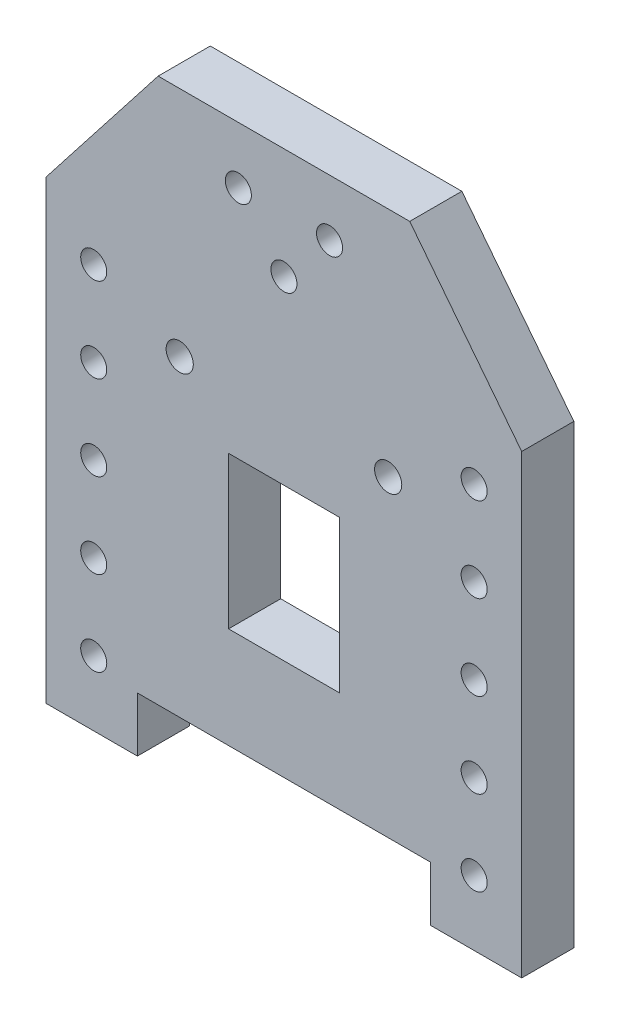
SolidWorks part; units mm, degrees
ref_plane "Plano frontal" through (0, 0, 0) normal (0, 0, 1) x (1, 0, 0)
ref_plane "Plano superior" through (0, 0, 0) normal (0, 1, 0) x (1, 0, 0)
ref_plane "Plano direito" through (0, 0, 0) normal (1, 0, 0) x (0, 0, -1)
sketch "Esboço1" plane through (0, 0, 0) normal (0, 0, 1) x (1, 0, 0)
  line L0 (0, 47.2571) -> (8.5, 47.2571)
  line L1 (0, 47.2571) -> (-8.5, 47.2571)
  line L2 (0, 23.9177) -> (8.5, 23.9177)
  line L3 (0, 23.9177) -> (-8.5, 23.9177)
  line L4 (0, 8.4) -> (0, 75) construction
  line L5 (0, 56.3545) -> (-16, 56.3545) construction
  line L6 (0, 56.3545) -> (16, 56.3545) construction
  line L7 (8.5, 47.2571) -> (8.5, 23.9177)
  line L8 (-8.5, 47.2571) -> (-8.5, 23.9177)
  line L20 (19.3117, 92) -> (-19.3117, 92)
  line L21 (-19.3117, 92) -> (-36.5, 70)
  line L22 (-36.5, 70) -> (-36.5, 0)
  line L23 (-36.5, 0) -> (-22.5, 0)
  line L24 (-22.5, 0) -> (-22.5, 8.4)
  line L25 (-22.5, 8.4) -> (22.5, 8.4)
  line L26 (22.5, 8.4) -> (22.5, 0)
  line L27 (22.5, 0) -> (36.5, 0)
  line L28 (36.5, 0) -> (36.5, 70)
  line L29 (36.5, 70) -> (19.3117, 92)
  circle A13 centre (0, 75) radius 2
  circle A14 centre (-7, 83.3) radius 2
  circle A15 centre (7, 83.3) radius 2
  circle A20 centre (-29.2, 10) radius 2
  circle A21 centre (29.2, 10) radius 2
  circle A26 centre (-16, 56.3545) radius 2.0867
  circle A27 centre (16, 56.3545) radius 2.0867
  point P31 (0, 23.9177)
  point P33 (0, 47.2571)
extrude "Ressalto-extrusão1" add sketch "Esboço1" along normal blind 8
sketch "Esboço2" plane through (0, 0, 0) normal (0, 0, -1) x (-1, 0, 0)
  circle A0 centre (29.2, 10) radius 2 construction
  circle A1 centre (29.2, 10) radius 2 construction
  circle A2 centre (29.2, 23) radius 2
  circle A3 centre (29.2, 36) radius 2
  circle A4 centre (29.2, 49) radius 2
  circle A5 centre (29.2, 62) radius 2
  circle A6 centre (-29.2, 49) radius 2
  circle A7 centre (-29.2, 36) radius 2
  circle A8 centre (-29.2, 62) radius 2
  circle A9 centre (-29.2, 10) radius 2 construction
  circle A11 centre (-29.2, 23) radius 2
  dimension "D1" = 5
extrude "Corte-extrusão1" cut sketch "Esboço2" against normal through all
